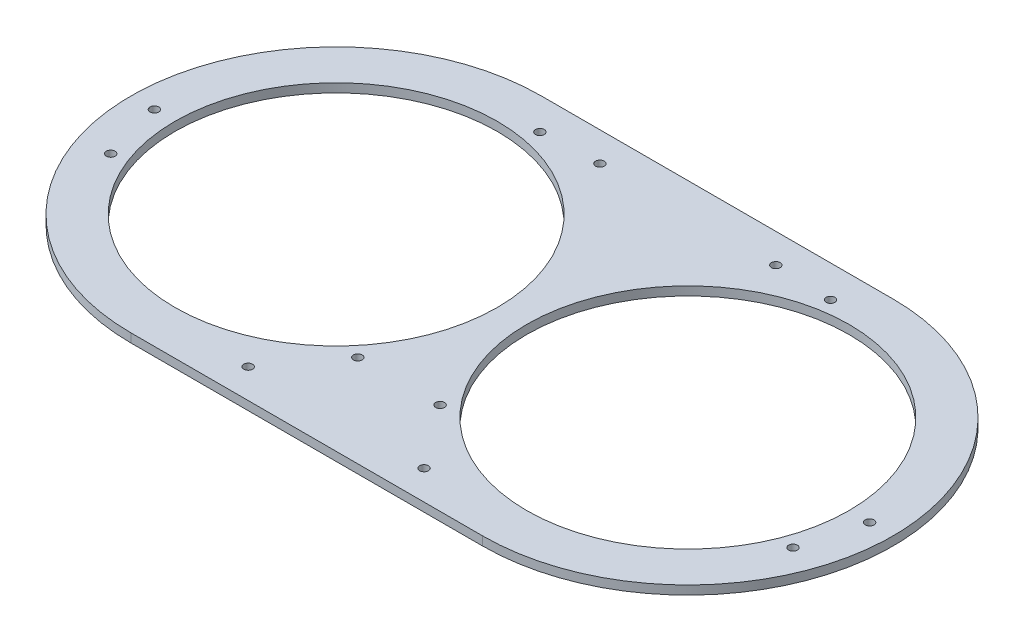
SolidWorks part; units mm, degrees
ref_plane "前视基准面" through (0, 0, 0) normal (0, 0, 1) x (1, 0, 0)
ref_plane "上视基准面" through (0, 0, 0) normal (0, 1, 0) x (1, 0, 0)
ref_plane "右视基准面" through (0, 0, 0) normal (1, 0, 0) x (0, 0, -1)
sketch "草图1" plane through (0, 0, 0) normal (0, 1, 0) x (1, 0, 0)
  line L0 (0, 0) -> (0, 89.0672) construction
  line L1 (-60, 0) -> (60, 0) construction
  line L2 (-60, 70) -> (60, 70)
  line L3 (-60, -70) -> (60, -70)
  line L4 (-90, 51.9615) -> (-60, 0) construction
  line L5 (-90, -51.9615) -> (-60, 0) construction
  line L6 (90, -51.9615) -> (60, 0) construction
  line L7 (90, 51.9615) -> (60, 0) construction
  line L8 (0, 0) -> (76.6344, 0) construction
  line L9 (-49.5811, 59.0885) -> (-60, 0) construction
  line L10 (-116.3816, -20.5212) -> (-60, 0) construction
  line L11 (-14.0373, -38.5673) -> (-60, 0) construction
  circle A0 centre (-60, 0) radius 55
  circle A1 centre (60, 0) radius 55
  arc A2 (-60, 70) -> (-60, -70) centre (-60, 0) ccw
  arc A3 (60, -70) -> (60, 70) centre (60, 0) ccw
  circle A4 centre (0, 0) radius 1.5 construction
  circle A5 centre (-90, 51.9615) radius 1.5 construction
  circle A6 centre (-90, -51.9615) radius 1.5 construction
  circle A7 centre (90, -51.9615) radius 1.5 construction
  circle A8 centre (90, 51.9615) radius 1.5 construction
  circle A9 centre (0, 0) radius 1.5 construction
  circle A10 centre (-122, 0) radius 1.5
  circle A11 centre (122, 0) radius 1.5
  circle A12 centre (-30, 60) radius 1.5
  circle A13 centre (30, 60) radius 1.5
  circle A14 centre (30, -60) radius 1.5
  circle A15 centre (-30, -60) radius 1.5
  circle A16 centre (-49.5811, 59.0885) radius 1.5
  circle A17 centre (-116.3816, -20.5212) radius 1.5
  circle A18 centre (-14.0373, -38.5673) radius 1.5
  circle A19 centre (14.0373, -38.5673) radius 1.5
  circle A20 centre (116.3816, -20.5212) radius 1.5
  circle A21 centre (49.5811, 59.0885) radius 1.5
  point P7 (0, 0)
  dimension "D1" = 110
  dimension "D2" = 60
  dimension "D3" = 15
  dimension "D4" = 3
  dimension "D5" = 60
  dimension "D6" = 60
  dimension "D7" = 3
  dimension "D9" = 3
  dimension "D10" = 60
  dimension "D12" = 3
  dimension "D13" = 62
  dimension "D14" = 62
  dimension "D15" = 3
  dimension "D16" = 3
  dimension "D18" = 60
  dimension "D19" = 3
  dimension "D22" = 3
  dimension "D23" = 60
  dimension "D25" = 3
  dimension "D8" = 120
  dimension "D11" = 120
  dimension "D17" = 30
  dimension "D20" = 60
  dimension "D21" = 80
  dimension "D24" = 120
  dimension "D26" = 60
  dimension "D27" = 120
extrude "凸台-拉伸2" add sketch "草图1" along normal blind 3 contours L3 A3 L2 A2 A13 A12 A11 A10 A7 A6 A5 A4 A1 A0 A8 A14 A15
